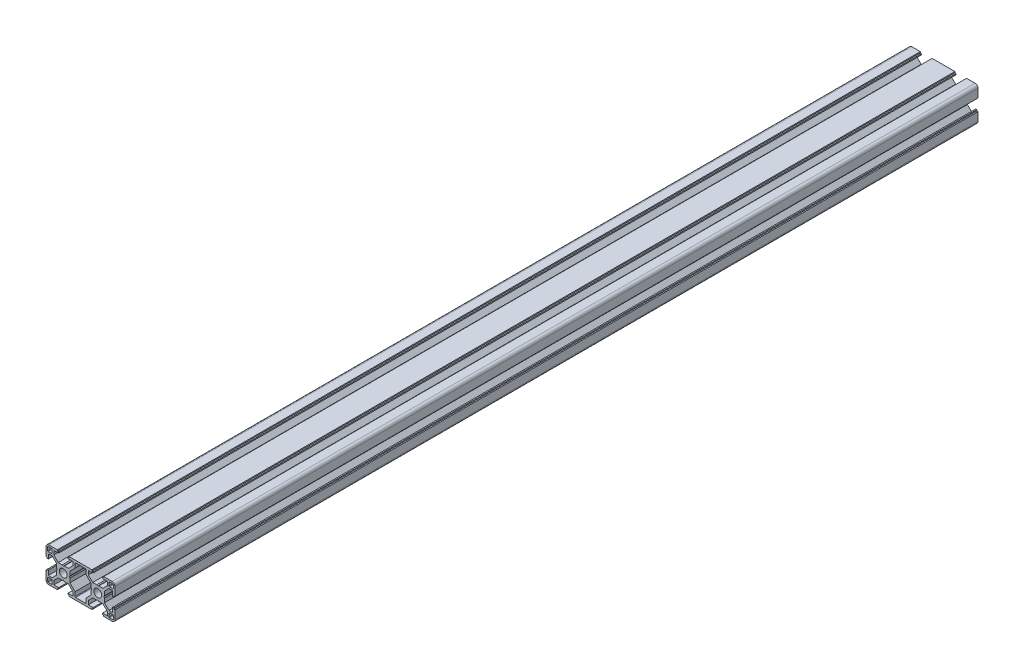
SolidWorks part; units mm, degrees
material "6063-T5"
ref_plane "Plan de face" through (0, 0, 0) normal (0, 0, 1) x (1, 0, 0)
ref_plane "Plan de dessus" through (0, 0, 0) normal (0, 1, 0) x (1, 0, 0)
ref_plane "Plan de droite" through (0, 0, 0) normal (1, 0, 0) x (0, 0, -1)
sketch "Esquisse1" plane through (0, 0, 0) normal (0, 0, 1) x (1, 0, 0)
  line L0 (16.032, 18.6935) -> (15.032, 18.6935)
  line L1 (15.032, 18.6935) -> (15.032, 19.6935)
  line L2 (16.032, 17.6935) -> (16.032, 18.6935)
  line L3 (-4.768, 19.6935) -> (15.032, 19.6935)
  line L4 (16.032, 17.6935) -> (11.882, 17.6935)
  line L5 (-4.768, 18.6935) -> (-4.768, 19.6935)
  line L6 (11.882, 14.3399) -> (11.882, 17.6935)
  line L7 (-5.768, 18.6935) -> (-4.768, 18.6935)
  line L8 (11.882, 14.3399) -> (15.7285, 10.4935)
  line L9 (-5.768, 17.6935) -> (-5.768, 18.6935)
  line L10 (19.266, 10.4935) -> (15.7285, 10.4935)
  line L11 (-5.768, 17.6935) -> (-1.618, 17.6935)
  line L12 (19.266, 10.4935) -> (20.132, 9.9935)
  line L13 (-1.618, 14.3399) -> (-1.618, 17.6935)
  line L14 (20.9981, 10.4935) -> (20.132, 9.9935)
  line L15 (-1.618, 14.3399) -> (-5.4644, 10.4935)
  line L16 (24.5356, 10.4935) -> (20.9981, 10.4935)
  line L17 (-9.0019, 10.4935) -> (-5.4644, 10.4935)
  line L18 (28.382, 14.3399) -> (24.5356, 10.4935)
  line L19 (-9.0019, 10.4935) -> (-9.868, 9.9935)
  line L20 (28.382, 14.3399) -> (28.382, 17.6935)
  line L21 (-10.734, 10.4935) -> (-9.868, 9.9935)
  line L22 (28.382, 17.6935) -> (24.232, 17.6935)
  line L23 (-14.2715, 10.4935) -> (-10.734, 10.4935)
  line L24 (24.232, 17.6935) -> (24.232, 18.6935)
  line L25 (-18.118, 14.3399) -> (-14.2715, 10.4935)
  line L26 (25.232, 18.6935) -> (24.232, 18.6935)
  line L27 (-18.118, 14.3399) -> (-18.118, 17.6935)
  line L28 (25.232, 18.6935) -> (25.232, 19.6935)
  line L29 (-18.118, 17.6935) -> (-13.968, 17.6935)
  line L30 (25.232, 19.6935) -> (32.632, 19.6935)
  line L31 (-13.968, 17.6935) -> (-13.968, 18.6935)
  line L32 (-14.968, 18.6935) -> (-13.968, 18.6935)
  line L33 (35.132, 17.1935) -> (35.132, 9.7935)
  line L34 (-14.968, 18.6935) -> (-14.968, 19.6935)
  line L35 (34.132, 9.7935) -> (35.132, 9.7935)
  line L36 (-22.368, 19.6935) -> (-14.968, 19.6935)
  line L37 (34.132, 8.7935) -> (34.132, 9.7935)
  line L38 (33.132, 8.7935) -> (34.132, 8.7935)
  line L39 (-24.868, 17.1935) -> (-24.868, 9.7935)
  line L40 (33.132, 8.7935) -> (33.132, 12.9435)
  line L41 (-23.868, 9.7935) -> (-24.868, 9.7935)
  line L42 (29.7785, 12.9435) -> (33.132, 12.9435)
  line L43 (-23.868, 8.7935) -> (-23.868, 9.7935)
  line L44 (29.7785, 12.9435) -> (25.932, 9.097)
  line L45 (-22.868, 8.7935) -> (-23.868, 8.7935)
  line L46 (25.932, 5.5595) -> (25.932, 9.097)
  line L47 (-22.868, 8.7935) -> (-22.868, 12.9435)
  line L48 (25.932, 5.5595) -> (25.432, 4.6935)
  line L49 (-19.5144, 12.9435) -> (-22.868, 12.9435)
  line L50 (25.932, 3.8275) -> (25.432, 4.6935)
  line L51 (-19.5144, 12.9435) -> (-15.668, 9.097)
  line L52 (25.932, 0.2899) -> (25.932, 3.8275)
  line L53 (-15.668, 5.5595) -> (-15.668, 9.097)
  line L54 (29.7785, -3.5565) -> (25.932, 0.2899)
  line L55 (-15.668, 5.5595) -> (-15.168, 4.6935)
  line L56 (29.7785, -3.5565) -> (33.132, -3.5565)
  line L57 (-15.668, 3.8275) -> (-15.168, 4.6935)
  line L58 (33.132, -3.5565) -> (33.132, 0.5935)
  line L59 (-15.668, 0.2899) -> (-15.668, 3.8275)
  line L60 (33.132, 0.5935) -> (34.132, 0.5935)
  line L61 (-19.5144, -3.5565) -> (-15.668, 0.2899)
  line L62 (34.132, -0.4065) -> (34.132, 0.5935)
  line L63 (-19.5144, -3.5565) -> (-22.868, -3.5565)
  line L64 (34.132, -0.4065) -> (35.132, -0.4065)
  line L65 (-22.868, -3.5565) -> (-22.868, 0.5935)
  line L66 (35.132, -0.4065) -> (35.132, -7.8065)
  line L67 (-22.868, 0.5935) -> (-23.868, 0.5935)
  line L68 (-23.868, -0.4065) -> (-23.868, 0.5935)
  line L69 (25.232, -10.3065) -> (32.632, -10.3065)
  line L70 (-23.868, -0.4065) -> (-24.868, -0.4065)
  line L71 (25.232, -9.3065) -> (25.232, -10.3065)
  line L72 (-24.868, -0.4065) -> (-24.868, -7.8065)
  line L73 (25.232, -9.3065) -> (24.232, -9.3065)
  line L74 (24.232, -8.3065) -> (24.232, -9.3065)
  line L75 (-22.368, -10.3065) -> (-14.968, -10.3065)
  line L76 (28.382, -8.3065) -> (24.232, -8.3065)
  line L77 (-14.968, -9.3065) -> (-14.968, -10.3065)
  line L78 (28.382, -4.953) -> (28.382, -8.3065)
  line L79 (-14.968, -9.3065) -> (-13.968, -9.3065)
  line L80 (28.382, -4.953) -> (24.5356, -1.1065)
  line L81 (-13.968, -8.3065) -> (-13.968, -9.3065)
  line L82 (24.5356, -1.1065) -> (20.9981, -1.1065)
  line L83 (-18.118, -8.3065) -> (-13.968, -8.3065)
  line L84 (20.9981, -1.1065) -> (20.132, -0.6065)
  line L85 (-18.118, -4.953) -> (-18.118, -8.3065)
  line L86 (19.266, -1.1065) -> (20.132, -0.6065)
  line L87 (-18.118, -4.953) -> (-14.2715, -1.1065)
  line L88 (19.266, -1.1065) -> (15.7285, -1.1065)
  line L89 (-14.2715, -1.1065) -> (-10.734, -1.1065)
  line L90 (11.882, -4.953) -> (15.7285, -1.1065)
  line L91 (-10.734, -1.1065) -> (-9.868, -0.6065)
  line L92 (11.882, -4.953) -> (11.882, -8.3065)
  line L93 (-9.0019, -1.1065) -> (-9.868, -0.6065)
  line L94 (16.032, -8.3065) -> (11.882, -8.3065)
  line L95 (-9.0019, -1.1065) -> (-5.4644, -1.1065)
  line L96 (16.032, -8.3065) -> (16.032, -9.3065)
  line L97 (-1.618, -4.953) -> (-5.4644, -1.1065)
  line L98 (16.032, -9.3065) -> (15.032, -9.3065)
  line L99 (-1.618, -4.953) -> (-1.618, -8.3065)
  line L100 (15.032, -9.3065) -> (15.032, -10.3065)
  line L101 (-5.768, -8.3065) -> (-1.618, -8.3065)
  line L102 (-4.768, -10.3065) -> (15.032, -10.3065)
  line L103 (-5.768, -8.3065) -> (-5.768, -9.3065)
  line L104 (-4.768, -9.3065) -> (-4.768, -10.3065)
  line L105 (-5.768, -9.3065) -> (-4.768, -9.3065)
  line L106 (-23.368, 14.9435) -> (-23.368, 17.6935)
  line L107 (-22.868, 18.1935) -> (-20.118, 18.1935)
  line L108 (-20.118, 14.4435) -> (-22.868, 14.4435)
  line L109 (-19.618, 17.6935) -> (-19.618, 14.9435)
  line L110 (-19.618, -5.5565) -> (-19.618, -8.3065)
  line L111 (-20.118, -8.8065) -> (-22.868, -8.8065)
  line L112 (-22.868, -5.0565) -> (-20.118, -5.0565)
  line L113 (-23.368, -8.3065) -> (-23.368, -5.5565)
  line L114 (14.332, 0.3255) -> (9.882, -4.1245)
  line L115 (9.882, -4.1245) -> (9.882, -7.8065)
  line L116 (14.332, 3.8275) -> (14.332, 0.3255)
  line L117 (14.832, 4.6935) -> (14.332, 3.8275)
  line L118 (9.382, -8.3065) -> (0.882, -8.3065)
  line L119 (14.332, 5.5595) -> (14.832, 4.6935)
  line L120 (14.332, 9.0615) -> (14.332, 5.5595)
  line L121 (0.382, -7.8065) -> (0.382, -4.1245)
  line L122 (9.882, 13.5115) -> (14.332, 9.0615)
  line L123 (0.382, -4.1245) -> (-4.068, 0.3255)
  line L124 (9.882, 17.1935) -> (9.882, 13.5115)
  line L125 (-4.068, 0.3255) -> (-4.068, 3.8275)
  line L126 (-4.068, 3.8275) -> (-4.568, 4.6935)
  line L127 (0.882, 17.6935) -> (9.382, 17.6935)
  line L128 (-4.568, 4.6935) -> (-4.068, 5.5595)
  line L129 (-4.068, 5.5595) -> (-4.068, 9.0615)
  line L130 (0.382, 13.5115) -> (0.382, 17.1935)
  line L131 (-4.068, 9.0615) -> (0.382, 13.5115)
  line L132 (29.882, 14.9435) -> (29.882, 17.6935)
  line L133 (30.382, 18.1935) -> (33.132, 18.1935)
  line L134 (33.132, 14.4435) -> (30.382, 14.4435)
  line L135 (33.632, 17.6935) -> (33.632, 14.9435)
  line L136 (29.882, -8.3065) -> (29.882, -5.5565)
  line L137 (30.382, -5.0565) -> (33.132, -5.0565)
  line L138 (33.132, -8.8065) -> (30.382, -8.8065)
  line L139 (33.632, -5.5565) -> (33.632, -8.3065)
  arc A0 (35.132, 17.1935) -> (32.632, 19.6935) centre (32.632, 17.1935) ccw
  arc A1 (-22.368, 19.6935) -> (-24.868, 17.1935) centre (-22.368, 17.1935) ccw
  arc A2 (32.632, -10.3065) -> (35.132, -7.8065) centre (32.632, -7.8065) ccw
  arc A3 (-24.868, -7.8065) -> (-22.368, -10.3065) centre (-22.368, -7.8065) ccw
  arc A4 (-22.868, 18.1935) -> (-23.368, 17.6935) centre (-22.868, 17.6935) ccw
  arc A5 (-23.368, 14.9435) -> (-22.868, 14.4435) centre (-22.868, 14.9435) ccw
  arc A6 (-19.618, 17.6935) -> (-20.118, 18.1935) centre (-20.118, 17.6935) ccw
  arc A7 (-20.118, 14.4435) -> (-19.618, 14.9435) centre (-20.118, 14.9435) ccw
  arc A8 (-20.118, -8.8065) -> (-19.618, -8.3065) centre (-20.118, -8.3065) ccw
  arc A9 (-19.618, -5.5565) -> (-20.118, -5.0565) centre (-20.118, -5.5565) ccw
  arc A10 (-23.368, -8.3065) -> (-22.868, -8.8065) centre (-22.868, -8.3065) ccw
  arc A11 (-22.868, -5.0565) -> (-23.368, -5.5565) centre (-22.868, -5.5565) ccw
  circle A12 centre (-9.868, 4.6935) radius 3.4
  arc A13 (9.382, -8.3065) -> (9.882, -7.8065) centre (9.382, -7.8065) ccw
  arc A14 (0.382, -7.8065) -> (0.882, -8.3065) centre (0.882, -7.8065) ccw
  arc A15 (9.882, 17.1935) -> (9.382, 17.6935) centre (9.382, 17.1935) ccw
  arc A16 (0.882, 17.6935) -> (0.382, 17.1935) centre (0.882, 17.1935) ccw
  circle A17 centre (20.132, 4.6935) radius 3.4
  arc A18 (30.382, 18.1935) -> (29.882, 17.6935) centre (30.382, 17.6935) ccw
  arc A19 (29.882, 14.9435) -> (30.382, 14.4435) centre (30.382, 14.9435) ccw
  arc A20 (33.632, 17.6935) -> (33.132, 18.1935) centre (33.132, 17.6935) ccw
  arc A21 (33.132, 14.4435) -> (33.632, 14.9435) centre (33.132, 14.9435) ccw
  arc A22 (30.382, -5.0565) -> (29.882, -5.5565) centre (30.382, -5.5565) ccw
  arc A23 (29.882, -8.3065) -> (30.382, -8.8065) centre (30.382, -8.3065) ccw
  arc A24 (33.632, -5.5565) -> (33.132, -5.0565) centre (33.132, -5.5565) ccw
  arc A25 (33.132, -8.8065) -> (33.632, -8.3065) centre (33.132, -8.3065) ccw
extrude "Extrusion1" add sketch "Esquisse1" along normal blind 750
